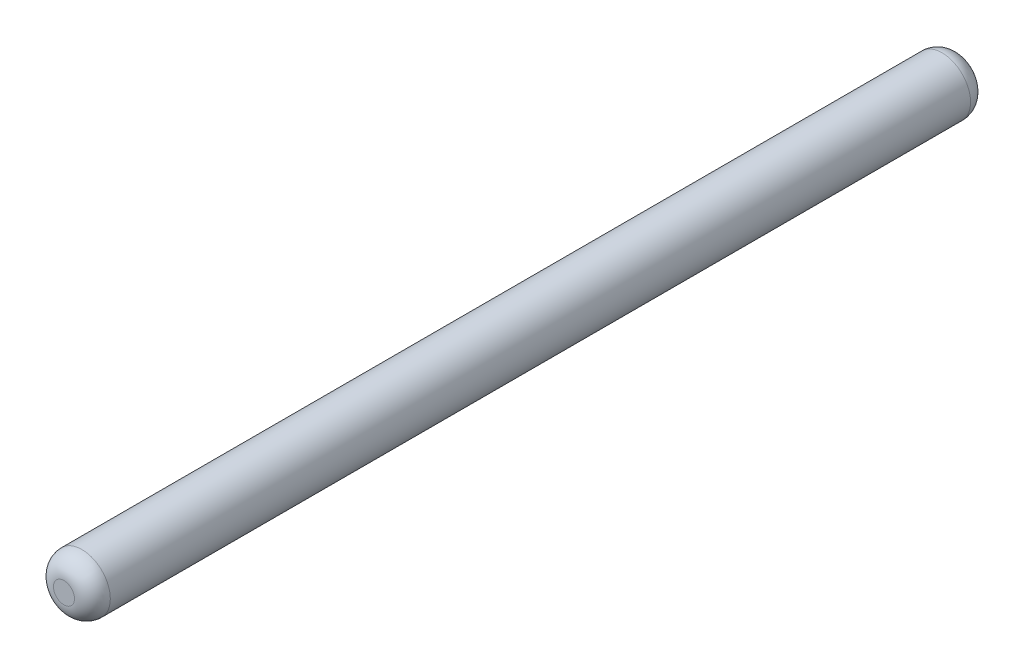
SolidWorks part; units mm, degrees
ref_plane "Front Plane" through (0, 0, 0) normal (0, 0, 1) x (1, 0, 0)
ref_plane "Top Plane" through (0, 0, 0) normal (0, 1, 0) x (1, 0, 0)
ref_plane "Right Plane" through (0, 0, 0) normal (1, 0, 0) x (0, 0, -1)
sketch "Sketch1" plane through (0, 0, 0) normal (0, 0, 1) x (1, 0, 0)
  circle A0 centre (0, 0) radius 3.175
  dimension "D1" = 6.35
extrude "Boss-Extrude1" add sketch "Sketch1" along normal blind 100
fillet "Fillet1" radius 2 2 edges at (3.175, 0, 100) (3.175, 0, 0)
